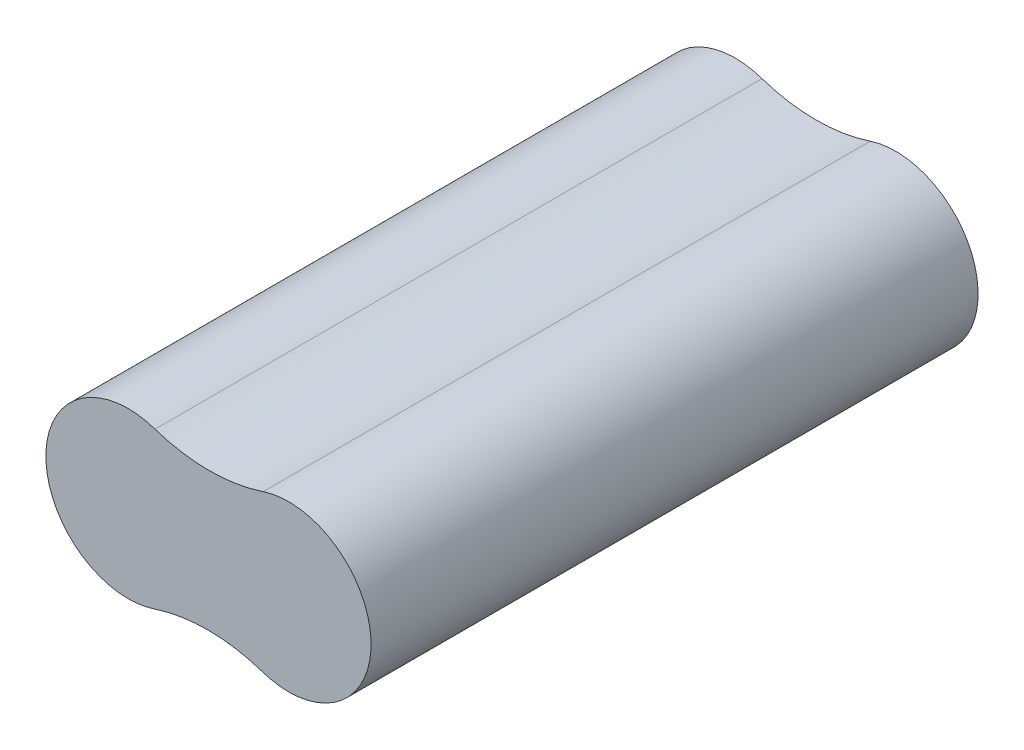
SolidWorks part; units mm, degrees
material "Silicon"
ref_plane "Front Plane" through (0, 0, 0) normal (0, 0, 1) x (1, 0, 0)
ref_plane "Top Plane" through (0, 0, 0) normal (0, 1, 0) x (1, 0, 0)
ref_plane "Right Plane" through (0, 0, 0) normal (1, 0, 0) x (0, 0, -1)
sketch "Sketch1" plane through (0, 0, 0) normal (0, 0, 1) x (1, 0, 0)
  line L0 (-18.9088, 0.0504) -> (-18.9088, 26.2625) construction
  line L1 (18.5912, -0.0795) -> (18.5912, 24.1932) construction
  arc A1 (6.0049, -8.9846) -> (6.1557, 9.035) centre (9.0915, 0) ccw
  arc A2 (-6.3223, 9.035) -> (6.1557, 9.035) centre (-0.0833, 27.7293) ccw
  arc A3 (-6.3223, -8.9342) -> (6.0049, -8.9846) centre (-0.2352, -27.6785) cw
  arc A4 (-6.3223, 9.035) -> (-6.3223, -8.9342) centre (-9.4088, 0.0504) ccw
  dimension "D3" = 19
  dimension "D1" = 9.5
  dimension "D2" = 37.5
extrude "Extrude2" add sketch "Sketch1" along normal blind 70
ref_plane "Plane1" through (0, 20, 0) normal (0, 1, 0) x (-1, 0, 0)
